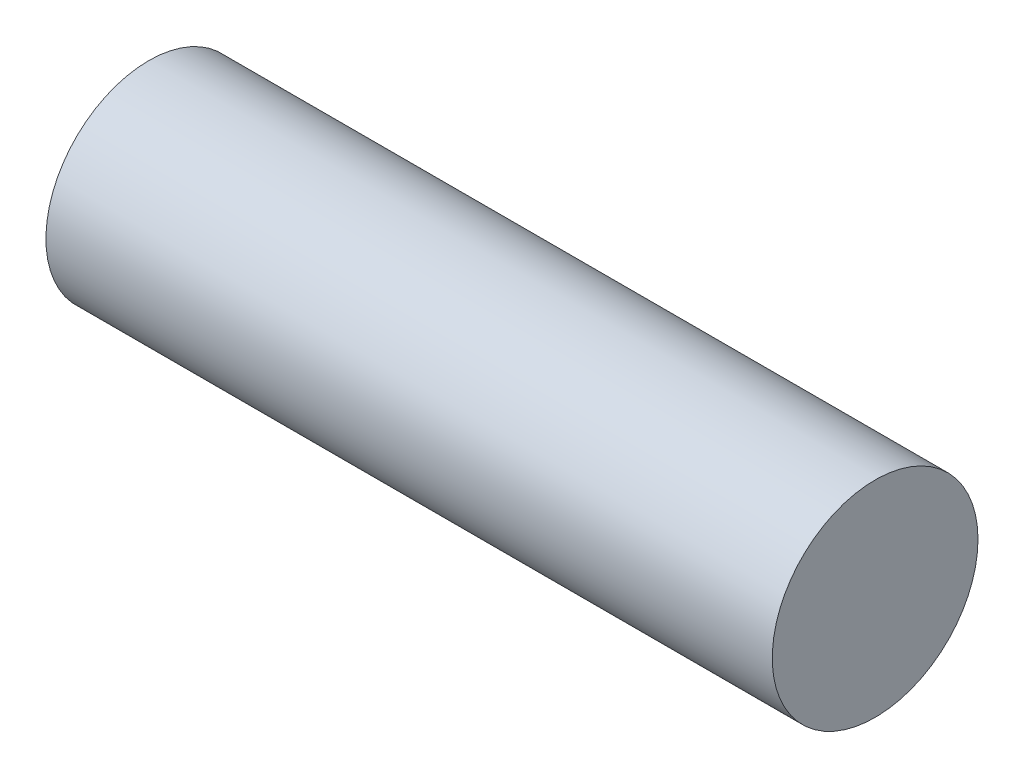
SolidWorks part; units mm, degrees
ref_plane "Ön Düzlem" through (0, 0, 0) normal (0, 0, 1) x (1, 0, 0)
ref_plane "Üst Düzlem" through (0, 0, 0) normal (0, 1, 0) x (1, 0, 0)
ref_plane "Sağ Düzlem" through (0, 0, 0) normal (1, 0, 0) x (0, 0, -1)
sketch "Sketch1" plane through (0, 0, 0) normal (0, 0, 1) x (1, 0, 0)
  line L0 (0, 1.65) -> (11.65, 1.65)
  line L1 (11.65, 1.65) -> (11.65, 0)
  line L2 (11.65, 0) -> (1.65, 0)
  arc A0 (1.65, 0) -> (0, 1.65) centre (0, 0) ccw
revolve "Revolve1" add sketch "Sketch1" angle 360 about L2
